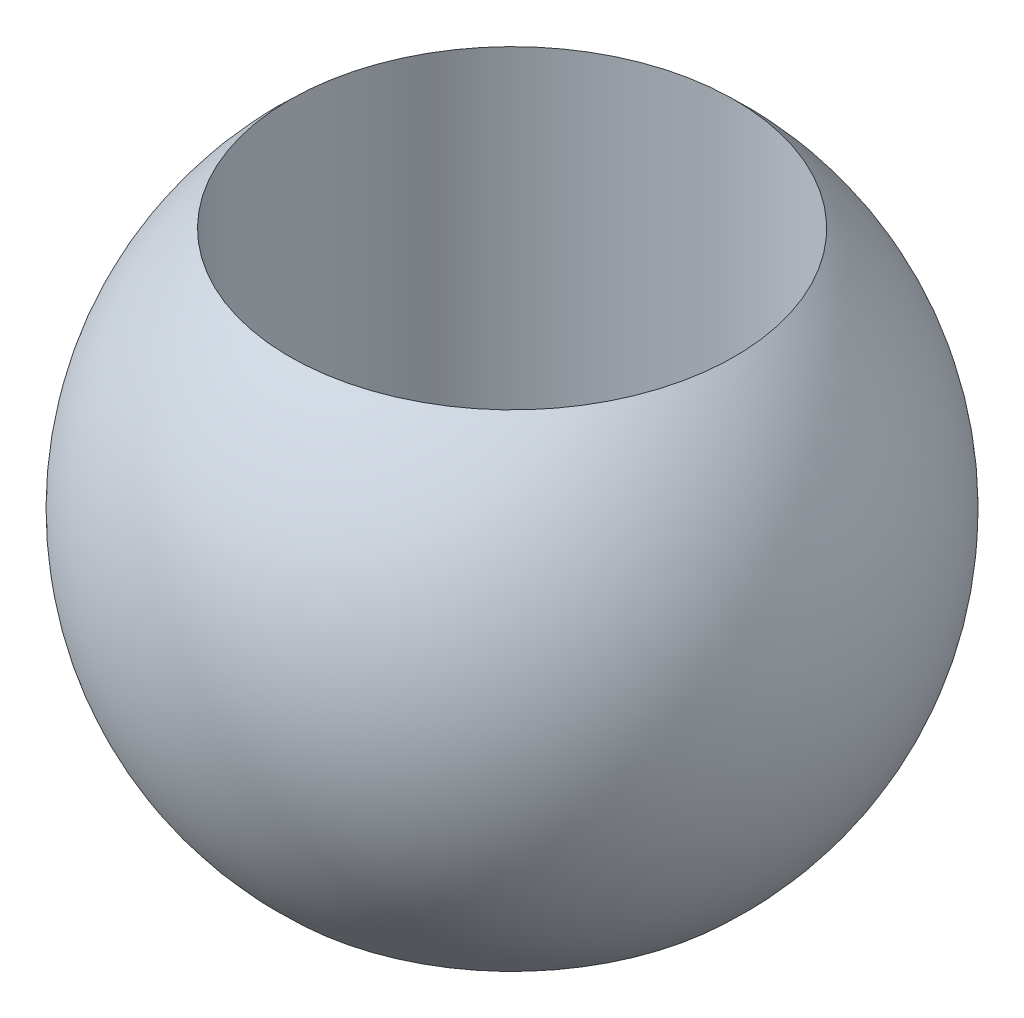
SolidWorks part; units mm, degrees
ref_plane "Front Plane" through (0, 0, 0) normal (0, 0, 1) x (1, 0, 0)
ref_plane "Top Plane" through (0, 0, 0) normal (0, 1, 0) x (1, 0, 0)
ref_plane "Right Plane" through (0, 0, 0) normal (1, 0, 0) x (0, 0, -1)
sketch "Sketch1" plane through (0, 0, 0) normal (0, 0, 1) x (1, 0, 0)
  line L0 (0, 2.032) -> (0, -2.032)
  line L1 (1.3716, 2.803) -> (1.3716, -2.9729)
  arc A0 (0, 2.032) -> (0, -2.032) centre (0, 0) cw
  point P4 (0, 0)
  dimension "D1" = 2.032
  dimension "D2" = 1.3716
revolve "Revolve1" add sketch "Sketch1" angle 360 about L0
